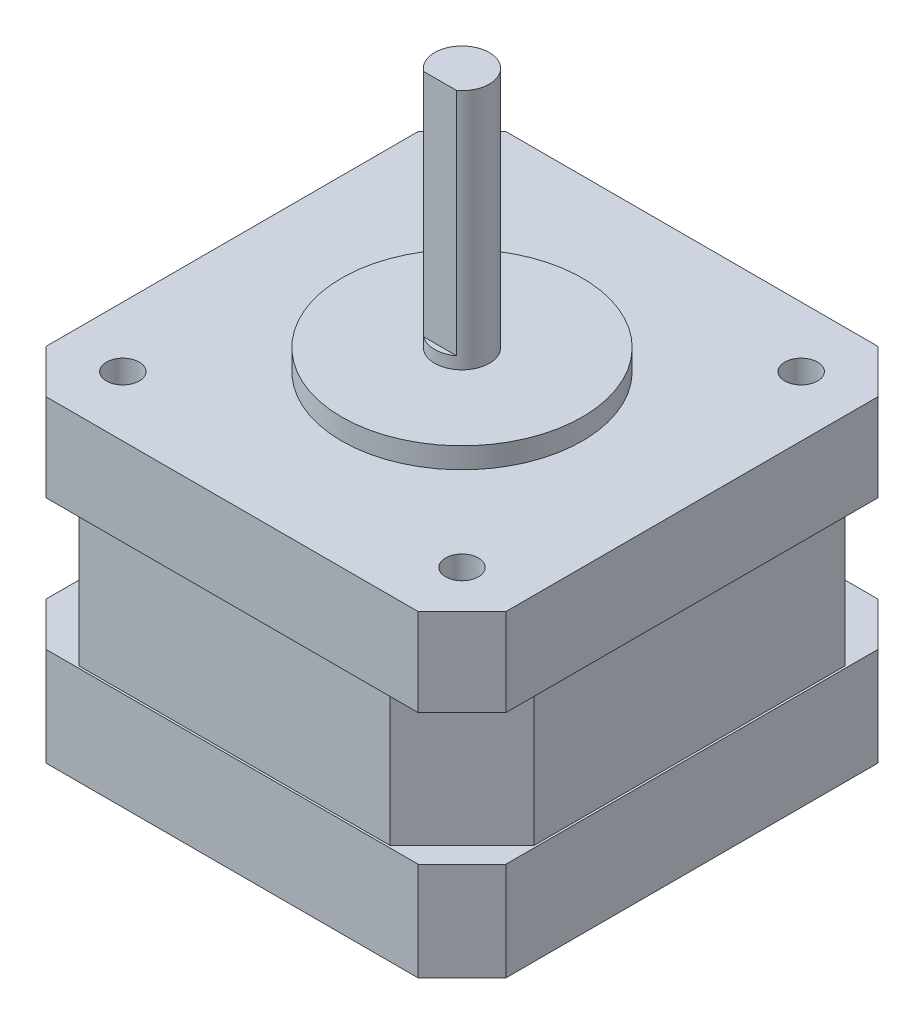
SolidWorks part; units mm, degrees
ref_plane "정면" through (0, 0, 0) normal (0, 0, 1) x (1, 0, 0)
ref_plane "윗면" through (0, 0, 0) normal (0, 1, 0) x (1, 0, 0)
ref_plane "우측면" through (0, 0, 0) normal (1, 0, 0) x (0, 0, -1)
ref_plane "평면1" through (-21, 0, 0) normal (-1, 0, 0) x (0, -1, 0)
sketch "스케치1" plane through (-21, 0, 0) normal (-1, 0, 0) x (0, -1, 0)
  line L0 (8, -21) -> (8, 21)
  line L1 (8, 21) -> (0, 21)
  line L2 (0, 21) -> (0, -21)
  line L3 (0, -21) -> (8, -21)
extrude "보스-돌출1" add sketch "스케치1" against normal blind 0.2
sketch "스케치2" plane through (-20.8, 0, 0) normal (1, 0, 0) x (0, 0, -1)
  line L0 (20.8, -8) -> (20.8, -20)
  line L1 (20.8, -20) -> (-20.8, -20)
  line L2 (-20.8, -20) -> (-20.8, -8)
  line L3 (-20.8, -8) -> (-21, -8)
  line L4 (-21, -8) -> (-21, 0)
  line L5 (-21, 0) -> (21, 0)
  line L6 (21, 0) -> (21, -8)
  line L7 (21, -8) -> (20.8, -8)
extrude "보스-돌출2" add sketch "스케치2" along normal blind 41.6
sketch "스케치3" plane through (20.8, 0, 0) normal (1, 0, 0) x (0, 0, -1)
  line L0 (21, -8) -> (-21, -8)
  line L1 (-21, -8) -> (-21, 0)
  line L2 (-21, 0) -> (21, 0)
  line L3 (21, 0) -> (21, -8)
extrude "보스-돌출3" add sketch "스케치3" along normal blind 0.2
ref_plane "평면2" through (0, -20, 0) normal (0, 1, 0) x (1, 0, 0)
sketch "스케치4" plane through (0, -20, 0) normal (0, 1, 0) x (1, 0, 0)
  line L0 (-21, -21) -> (21, -21)
  line L1 (21, -21) -> (21, 21)
  line L2 (21, 21) -> (-21, 21)
  line L3 (-21, 21) -> (-21, -21)
extrude "보스-돌출4" add sketch "스케치4" against normal blind 9
sketch "스케치5" plane through (0, 0, 0) normal (0, 1, 0) x (-1, 0, 0)
  circle A0 centre (0, 0) radius 11
extrude "보스-돌출5" add sketch "스케치5" along normal blind 1.9
sketch "스케치6" plane through (0, 1.9, 0) normal (0, 1, 0) x (-1, 0, 0)
  circle A0 centre (0, 0) radius 2.5
extrude "보스-돌출6" add sketch "스케치6" along normal blind 22.1
sketch "스케치7" plane through (0, 24, 0) normal (0, 1, 0) x (-1, 0, 0)
  line L0 (-1.5, 2) -> (1.5, 2)
  arc A0 (1.5, 2) -> (-1.5, 2) centre (0, 0) ccw
extrude "컷-돌출1" cut sketch "스케치7" against normal blind 21
sketch "스케치8" plane through (0, 0, 0) normal (0, 0, 1) x (1, 0, 0)
  line L0 (2.5, 0) -> (0, 0)
  line L1 (0, 0) -> (0, -8)
  line L2 (0, -8) -> (2.5, -8)
  line L3 (2.5, -8) -> (2.5, 0)
  line L4 (0, 0) -> (0, -8) construction
revolve "컷-회전1" cut sketch "스케치8" angle 360 about L4
hole_wizard "Ø5.0 (5) 지름 구멍1" positions "스케치10" profile "스케치9" hole size "Ø5.0" standard "Ansi Metric"
sketch "스케치10" plane through (0, -29, 0) normal (0, -1, 0) x (-1, 0, 0)
  point P0 (0, 0)
sketch "스케치9" plane through (0, -29, 0) normal (1, 0, 0) x (0, 0, -1)
  line L0 (0, 0) -> (0, 5)
  line L1 (0, 5) -> (2.5, 5)
  line L2 (2.5, 5) -> (2.5, 0)
  line L5 (2.5, 0) -> (0, 0)
  line L10 (0, 5) -> (-2.5, 5) construction
  line L11 (0, -6.35) -> (0, 107.95) construction
  dimension "구멍 지름" = 5
  dimension "구멍 깊이" = 5
  dimension "드릴 각도" = 180
hole_wizard "Ø3.0 (3) 지름 구멍1" positions "스케치12" profile "스케치11" hole size "Ø3.0" standard "Ansi Metric"
sketch "스케치12" plane through (0, 0, 0) normal (0, 1, 0) x (1, 0, 0)
  point P0 (-15.5, 15.5)
  point P1 (15.5, -15.5)
  point P2 (15.5, 15.5)
  point P3 (-15.5, -15.5)
sketch "스케치11" plane through (-15.5, 0, -15.5) normal (1, 0, 0) x (0, 0, 1)
  line L0 (0, 0) -> (0, 4)
  line L1 (0, 4) -> (1.5, 4)
  line L2 (1.5, 4) -> (1.5, 0)
  line L5 (1.5, 0) -> (0, 0)
  line L10 (0, 4) -> (-1.5, 4) construction
  line L11 (0, -6.35) -> (0, 107.95) construction
  dimension "구멍 지름" = 3
  dimension "구멍 깊이" = 4
  dimension "드릴 각도" = 180
chamfer "모따기1" distance 6.6 angle 45 4 edges at (-20.8, -14, -20.8) (20.8, -14, -20.8) (-20.8, -14, 20.8) (20.8, -14, 20.8)
chamfer "모따기2" distance 4 angle 45 8 edges at (21, -24.5, 21) (-21, -24.5, -21) (-21, -4, 21) (-21, -4, -21) (21, -24.5, -21) (21, -4, -21) (-21, -24.5, 21) (21, -4, 21)
